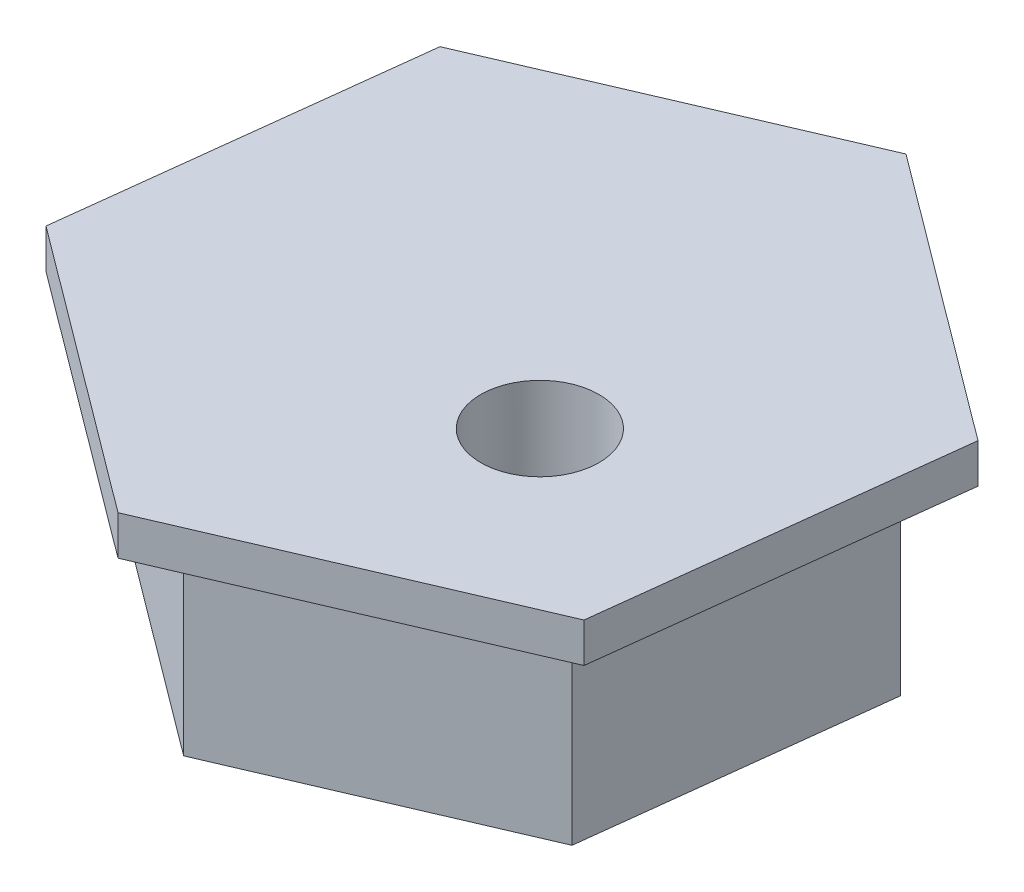
SolidWorks part; units mm, degrees
ref_plane "Front Plane" through (0, 0, 0) normal (0, 0, 1) x (1, 0, 0)
ref_plane "Top Plane" through (0, 0, 0) normal (0, 1, 0) x (1, 0, 0)
ref_plane "Right Plane" through (0, 0, 0) normal (1, 0, 0) x (0, 0, -1)
sketch "Sketch1" plane through (0, 0, 0) normal (0, 1, 0) x (1, 0, 0)
  line L1 (6.0095, -4.4873) -> (6.8909, 2.9607)
  line L2 (6.8909, 2.9607) -> (0.8814, 7.448)
  line L3 (0.8814, 7.448) -> (-6.0095, 4.4873)
  line L4 (-6.0095, 4.4873) -> (-6.8909, -2.9607)
  line L5 (-6.8909, -2.9607) -> (-0.8814, -7.448)
  line L6 (-0.8814, -7.448) -> (6.0095, -4.4873)
  circle A0 centre (0, 0) radius 6.4952 construction
  circle A1 centre (2.4457, -1.7388) radius 1.5
  dimension "D2" = 3
  dimension "D1" = 15
extrude "Boss-Extrude1" add sketch "Sketch1" along normal blind 6 contours L5 L6 L1 L2 L3 L4 A1
sketch "Sketch2" plane through (0, 6, 0) normal (0, 1, 0) x (1, 0, 0)
  line L1 (6.8909, 2.9607) -> (0.8814, 7.448) construction
  line L2 (8.2691, 3.5528) -> (1.0577, 8.9376)
  line L3 (1.0577, 8.9376) -> (-7.2114, 5.3848)
  line L4 (-7.2114, 5.3848) -> (-8.2691, -3.5528)
  line L5 (-8.2691, -3.5528) -> (-1.0577, -8.9376)
  line L6 (-1.0577, -8.9376) -> (7.2114, -5.3848)
  line L8 (7.2114, -5.3848) -> (8.2691, 3.5528)
  circle A0 centre (0, 0) radius 7.7942 construction
  dimension "D1" = 1.5
extrude "Boss-Extrude2" add sketch "Sketch2" against normal blind 1
sketch "Sketch4" plane through (0, 5, 0) normal (0, -1, 0) x (1, 0, 0)
  circle A0 centre (2.4457, 1.7388) radius 1.5
extrude "Cut-Extrude1" cut sketch "Sketch4" against normal blind 1
